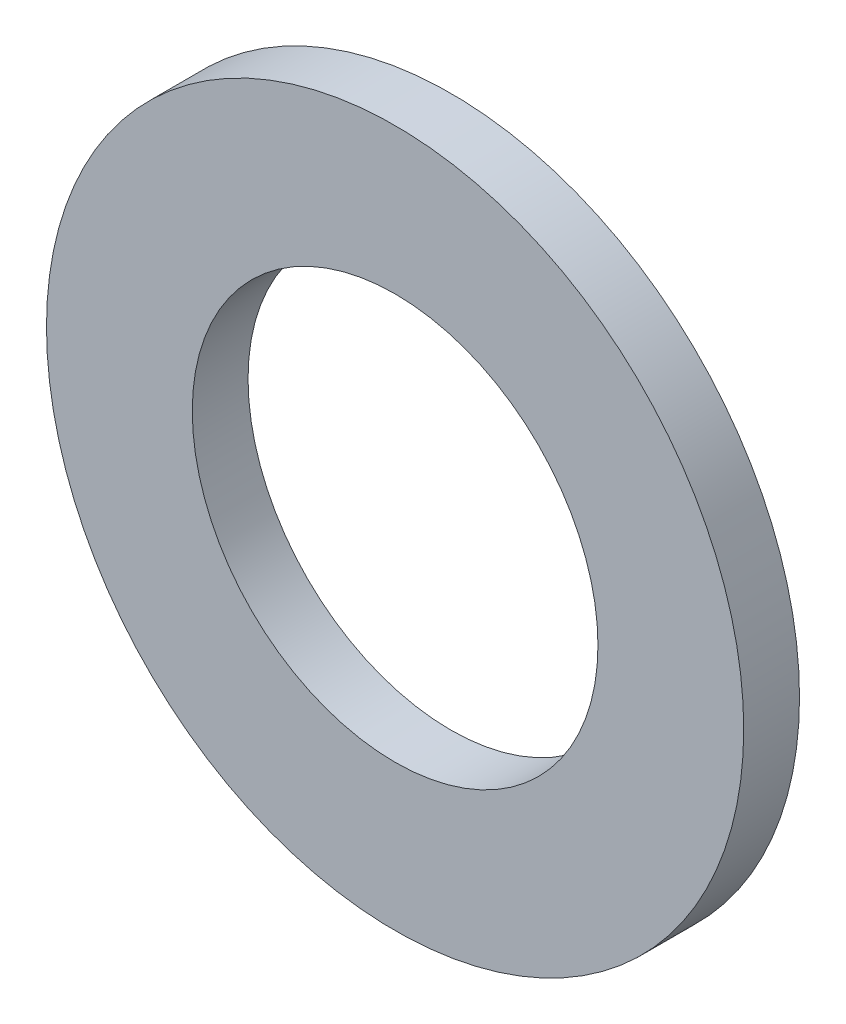
SolidWorks part; units mm, degrees
material "Plain Carbon Steel"
ref_plane "Front Plane" through (0, 0, 0) normal (0, 0, 1) x (1, 0, 0)
ref_plane "Top Plane" through (0, 0, 0) normal (0, 1, 0) x (1, 0, 0)
ref_plane "Right Plane" through (0, 0, 0) normal (1, 0, 0) x (0, 0, -1)
sketch "Sketch1" plane through (0, 0, 0) normal (0, 0, 1) x (1, 0, 0)
  circle A0 centre (0, 0) radius 3.4925
  circle A1 centre (0, 0) radius 2.032
  dimension "D1" = 6.985
  dimension "D2" = 4.064
extrude "Boss-Extrude1" add sketch "Sketch1" along normal mid plane 0.5588
